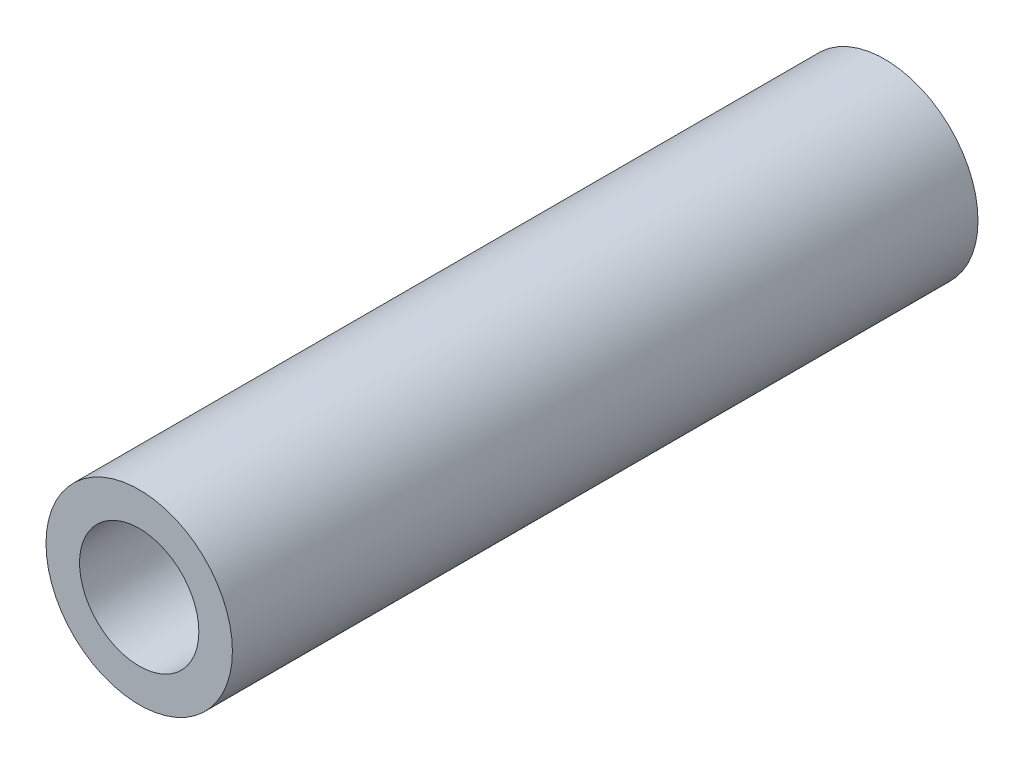
SolidWorks part; units mm, degrees
ref_plane "Front" through (0, 0, 0) normal (0, 0, 1) x (1, 0, 0)
ref_plane "Top" through (0, 0, 0) normal (0, 1, 0) x (1, 0, 0)
ref_plane "Right" through (0, 0, 0) normal (1, 0, 0) x (0, 0, -1)
sketch "Sketch1" plane through (0, 0, 0) normal (0, 0, 1) x (1, 0, 0)
  circle A0 centre (0, 0) radius 2.5
  circle A1 centre (0, 0) radius 1.6
extrude "Boss-Extrude1" add sketch "Sketch1" along normal blind 20
